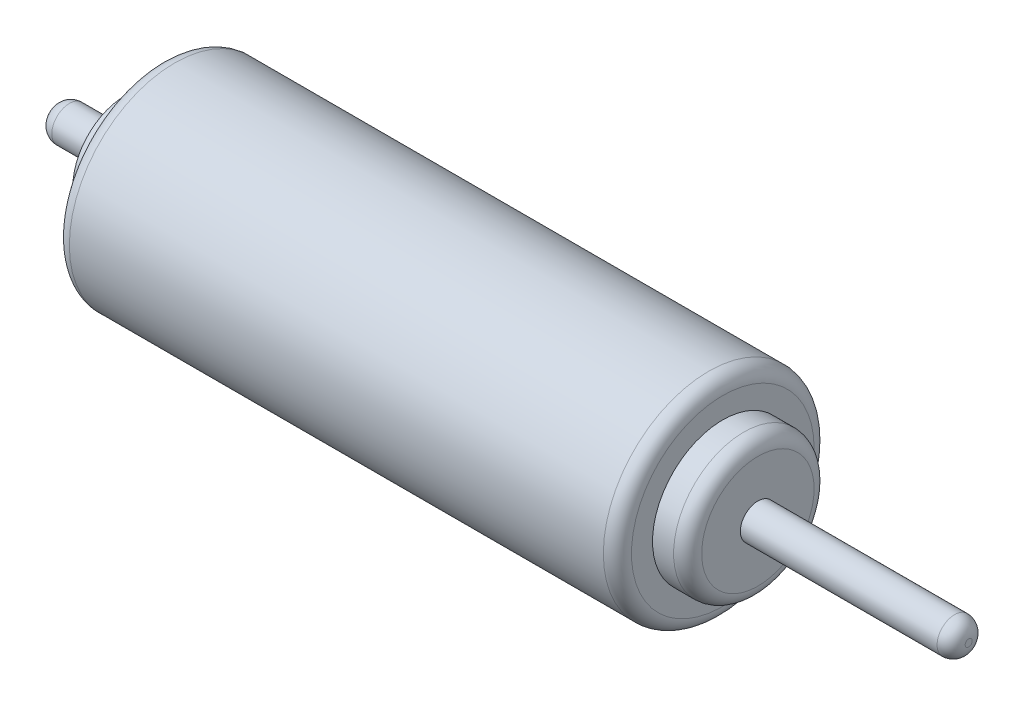
SolidWorks part; units mm, degrees
ref_plane "Front Plane" through (0, 0, 0) normal (0, 0, 1) x (1, 0, 0)
ref_plane "Top Plane" through (0, 0, 0) normal (0, 1, 0) x (1, 0, 0)
ref_plane "Right Plane" through (0, 0, 0) normal (1, 0, 0) x (0, 0, -1)
sketch "Sketch1" plane through (0, 0, 0) normal (1, 0, 0) x (0, 0, -1)
  circle A0 centre (0, 0) radius 15
  dimension "D1" = 30
extrude "Boss-Extrude1" add sketch "Sketch1" along normal blind 80
sketch "Sketch2" plane through (80, 0, 0) normal (1, 0, 0) x (0, 0, -1)
  circle A0 centre (0, 0) radius 10
  dimension "D1" = 20
extrude "Boss-Extrude2" add sketch "Sketch2" along normal blind 5
sketch "Sketch3" plane through (85, 0, 0) normal (1, 0, 0) x (0, 0, -1)
  circle A0 centre (0, 0) radius 2.5
  dimension "D1" = 5
extrude "Boss-Extrude3" add sketch "Sketch3" along normal blind 30
fillet "Fillet1" radius 2 1 edges at (80, 0, -15)
fillet "Fillet2" radius 2 1 edges at (85, 0, -10)
fillet "Fillet3" radius 2 1 edges at (0, 0, -15)
sketch "Sketch4" plane through (0, 0, 0) normal (-1, 0, 0) x (0, 0, 1)
  circle A0 centre (0, 0) radius 7.5
  dimension "D1" = 15
extrude "Boss-Extrude5" add sketch "Sketch4" along normal blind 5
sketch "Sketch5" plane through (-5, 0, 0) normal (-1, 0, 0) x (0, 0, 1)
  circle A0 centre (0, 0) radius 2.5
  dimension "D1" = 5
extrude "Boss-Extrude6" add sketch "Sketch5" along normal blind 10
fillet "Fillet4" radius 2 2 edges at (115, 0, -2.5) (-15, 0, 2.5)
